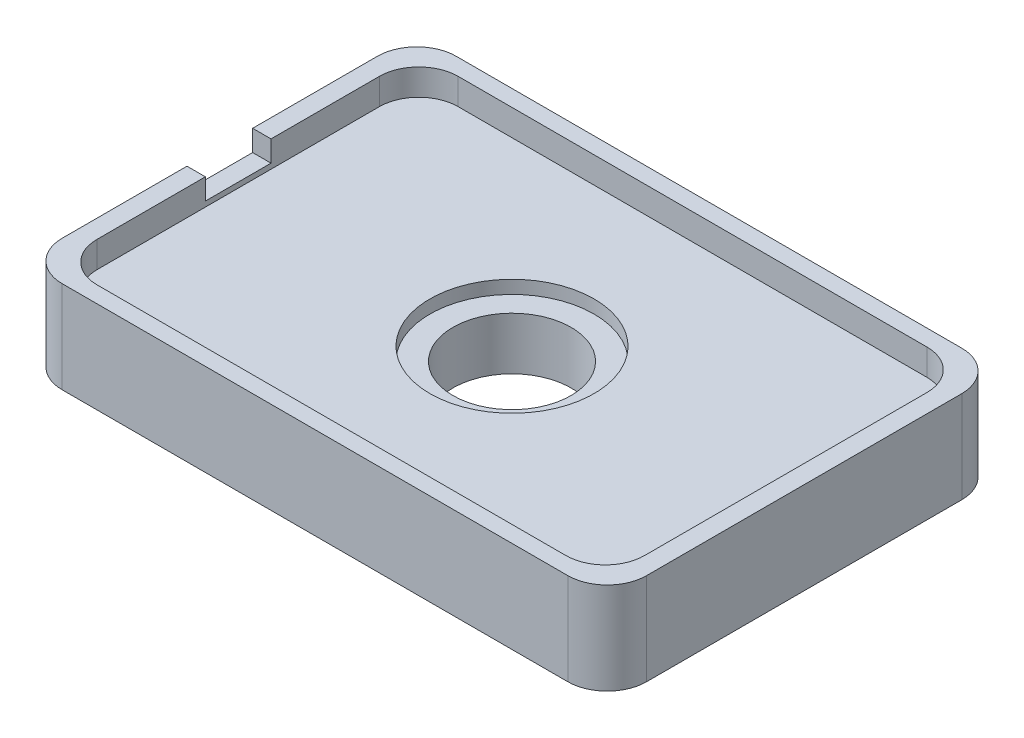
SolidWorks part; units mm, degrees
ref_plane "Front Plane" through (0, 0, 0) normal (0, 0, 1) x (1, 0, 0)
ref_plane "Top Plane" through (0, 0, 0) normal (0, 1, 0) x (1, 0, 0)
ref_plane "Right Plane" through (0, 0, 0) normal (1, 0, 0) x (0, 0, -1)
sketch "Sketch1" plane through (0, 0, 0) normal (0, 1, 0) x (1, 0, 0)
  line L1 (-22.25, 15) -> (22.25, 15)
  line L2 (-22.25, 15) -> (-22.25, -15)
  line L3 (-22.25, -15) -> (22.25, -15)
  line L4 (22.25, 15) -> (22.25, -15)
  line L5 (-22.25, 15) -> (22.25, -15) construction
  line L6 (-22.25, -15) -> (22.25, 15) construction
  point P0 (0, 0)
  dimension "D1" = 30
  dimension "D2" = 44.5
extrude "Boss-Extrude1" add sketch "Sketch1" against normal blind 5
sketch "Sketch2" plane through (0, 0, 0) normal (0, 1, 0) x (1, 0, 0)
  circle A0 centre (0, 0) radius 4.5
  dimension "D1" = 9
extrude "Cut-Extrude1" cut sketch "Sketch2" against normal up to next
sketch "Sketch5" plane through (0, 0, 0) normal (0, 1, 0) x (1, 0, 0)
  line L0 (-22.25, 15) -> (-22.25, -15) construction
  line L1 (20.85, -13.75) -> (-20.85, -13.75)
  line L2 (20.85, -13.75) -> (20.85, 13.75)
  line L3 (20.85, 13.75) -> (-20.85, 13.75)
  line L4 (-20.85, -13.75) -> (-20.85, 13.75)
  line L5 (20.85, -13.75) -> (-20.85, 13.75) construction
  line L6 (20.85, 13.75) -> (-20.85, -13.75) construction
  line L7 (-22.25, -15) -> (22.25, -15) construction
  line L12 (22.25, -15) -> (22.25, 15)
  line L13 (22.25, 15) -> (-22.25, 15)
  line L14 (-22.25, 15) -> (-22.25, -15)
  line L15 (-22.25, -15) -> (22.25, -15)
  line L16 (22.25, -15) -> (22.25, 15)
  line L17 (22.25, 15) -> (-22.25, 15)
  line L18 (-22.25, 15) -> (-22.25, -15)
  line L19 (-22.25, -15) -> (22.25, -15)
  point P0 (0, 0)
  dimension "D1" = 1.4
  dimension "D2" = 1.25
  dimension "D3" = 0
extrude "Boss-Extrude2" add sketch "Sketch5" along normal blind 2
sketch "Sketch6" plane through (-22.25, 0, 0) normal (-1, 0, 0) x (0, 0, 1)
  line L0 (-15, 2) -> (15, 2) construction
  line L1 (2.5, 2) -> (-2.5, 2)
  line L2 (2.5, 2) -> (2.5, 0.4)
  line L3 (2.5, 0.4) -> (-2.5, 0.4)
  line L4 (-2.5, 2) -> (-2.5, 0.4)
  line L5 (15, 2) -> (2.5, 2) construction
  line L6 (-2.5, 2) -> (-15, 2) construction
  dimension "D1" = 1.6
  dimension "D2" = 5
extrude "Cut-Extrude5" cut sketch "Sketch6" against normal up to next
fillet "Fillet1" radius 3 8 edges at (20.85, 1, -13.75) (-20.85, 1, -13.75) (-20.85, 1, 13.75) (20.85, 1, 13.75) (-22.25, -1.5, -15) (-22.25, -1.5, 15) (22.25, -1.5, 15) (22.25, -1.5, -15)
sketch "Sketch7" plane through (0, 0, 0) normal (0, 1, 0) x (1, 0, 0)
  circle A0 centre (0, 0) radius 6.25
  dimension "D1" = 12.5
extrude "Cut-Extrude6" cut sketch "Sketch7" against normal blind 1
